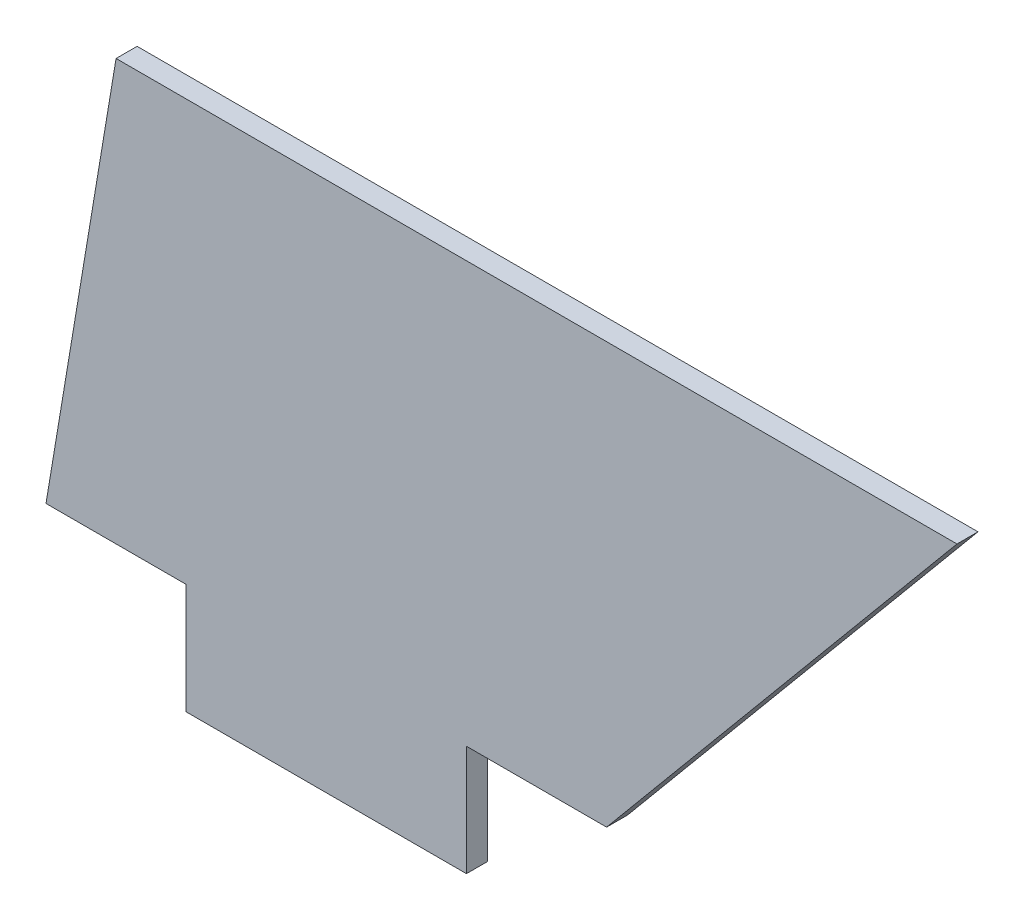
SolidWorks part; units mm, degrees
ref_plane "Front Plane" through (0, 0, 0) normal (0, 0, 1) x (1, 0, 0)
ref_plane "Top Plane" through (0, 0, 0) normal (0, 1, 0) x (1, 0, 0)
ref_plane "Right Plane" through (0, 0, 0) normal (1, 0, 0) x (0, 0, -1)
sketch "Sketch1" plane through (0, 0, 0) normal (0, 0, 1) x (1, 0, 0)
  line L0 (0, 0) -> (10, 0)
  line L1 (10, 0) -> (10, -7.875)
  line L2 (10, -7.875) -> (30, -7.875)
  line L3 (30, -7.875) -> (30, 0)
  line L4 (30, 0) -> (40, 0)
  line L5 (40, 0) -> (65, 30)
  line L6 (65, 30) -> (5, 30)
  line L7 (5, 30) -> (0, 0)
  dimension "D1" = 40
  dimension "D2" = 7.875
  dimension "D3" = 20
  dimension "D4" = 30
  dimension "D5" = 60
  dimension "D6" = 5
  dimension "D7" = 10
extrude "Boss-Extrude1" add sketch "Sketch1" along normal blind 1.5
